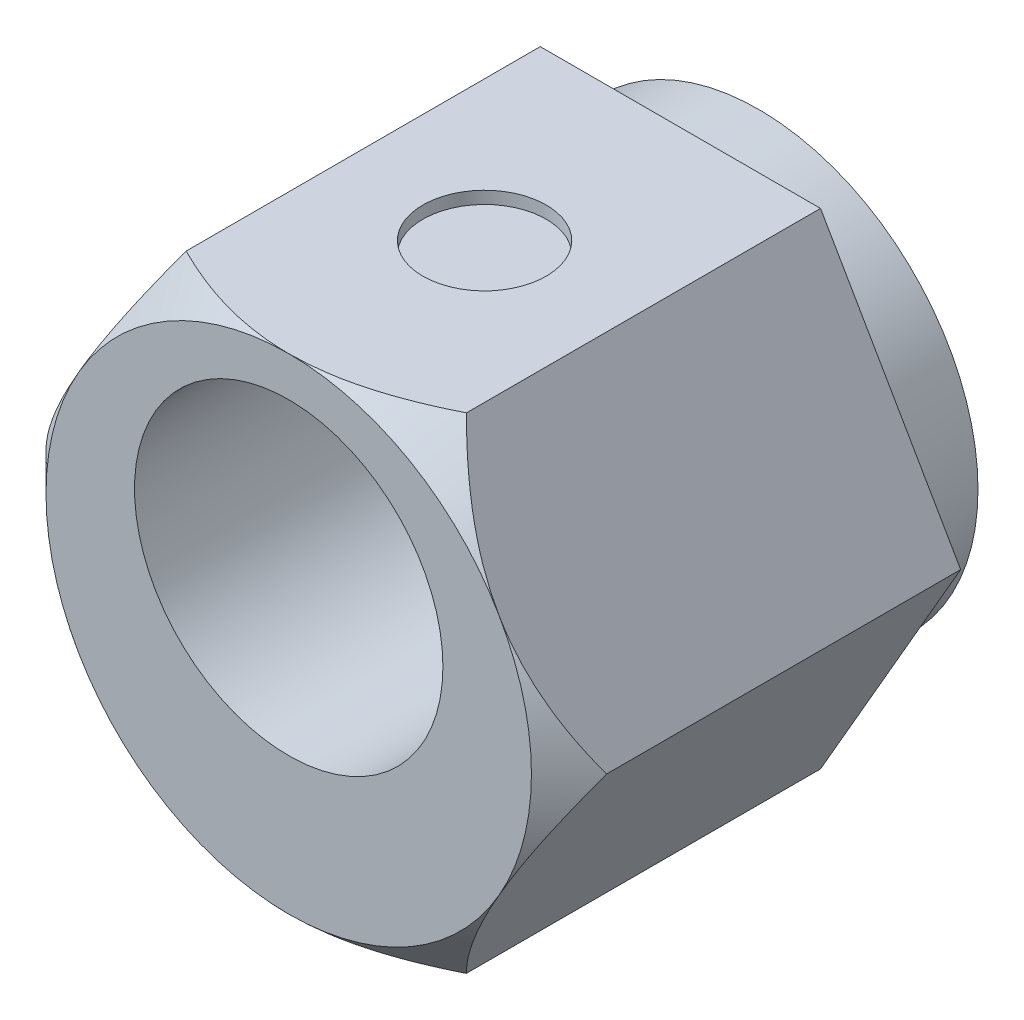
SolidWorks part; units mm, degrees
material "1.5714 (16NiCr4)"
ref_plane "Plane1" through (0, 0, 0) normal (0, 0, 1) x (1, 0, 0)
ref_plane "Plane2" through (0, 0, 0) normal (0, 1, 0) x (1, 0, 0)
ref_plane "Plane3" through (0, 0, 0) normal (1, 0, 0) x (0, 0, -1)
sketch "Sketch1" plane through (0, 0, 0) normal (0, 0, 1) x (1, 0, 0)
  circle A0 centre (0, 0) radius 3.555
  dimension "D1" = 7.11
extrude "Extrude1" add sketch "Sketch1" against normal blind 1.27
sketch "Sketch2" plane through (0, 0, 0) normal (0, 0, 1) x (1, 0, 0)
  line L1 (4.5437, 0) -> (2.2719, 3.935)
  line L2 (2.2719, 3.935) -> (-2.2719, 3.935)
  line L3 (-2.2719, 3.935) -> (-4.5437, 0)
  line L4 (-4.5437, 0) -> (-2.2719, -3.935)
  line L5 (-2.2719, -3.935) -> (2.2719, -3.935)
  line L6 (2.2719, -3.935) -> (4.5437, 0)
  circle A0 centre (0, 0) radius 3.935 construction
  dimension "D1" = 7.87
extrude "ICE1" add sketch "Sketch2" along normal blind 6.35
sketch "Sketch3" plane through (0, 0, 6.35) normal (0, 0, 1) x (1, 0, 0)
  circle A0 centre (0, 0.79) radius 2.5
  dimension "D1" = 5
  dimension "D2" = 0.79
extrude "ICE2" cut sketch "Sketch3" against normal through all
sketch "Sketch4" plane through (0, 3.935, 0) normal (0, 1, 0) x (1, 0, 0)
  line L0 (-2.2719, 0) -> (2.2719, -6.35) construction
  circle A0 centre (0, -3.175) radius 1
  dimension "D1" = 2
extrude "ICE3" cut sketch "Sketch4" against normal blind 0.2
ref_plane "Plane4" through (0, 0, 0) normal (-0.5, 0.866, 0) x (-0.866, -0.5, 0)
sketch "Sketch5" plane through (0, 0, 0) normal (-0.5, 0.866, 0) x (-0.866, -0.5, 0)
  line L0 (-3.935, 6.35) -> (-10.285, 0)
  line L1 (-10.285, 0) -> (-10.285, 6.35)
  line L2 (-10.285, 6.35) -> (-3.935, 6.35)
  line L3 (-3.935, 6.35) -> (-3.935, 0) construction
  line L4 (-3.935, 0) -> (0, 0) construction
  line L5 (0, 0) -> (0, 6.35) construction
  dimension "D1" = 45
revolve "RevCut1" cut sketch "Sketch5" angle 360 about L5
